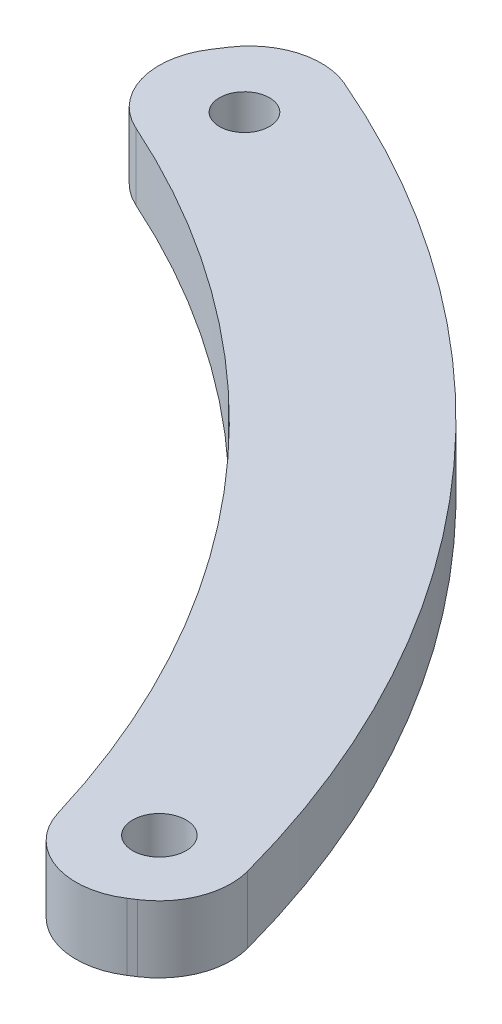
SolidWorks part; units mm, degrees
material "ABS generico"
ref_plane "Piano frontale" through (0, 0, 0) normal (0, 0, 1) x (1, 0, 0)
ref_plane "Piano superiore" through (0, 0, 0) normal (0, 1, 0) x (1, 0, 0)
ref_plane "Piano destro" through (0, 0, 0) normal (1, 0, 0) x (0, 0, -1)
sketch "Schizzo1" plane through (0, 0, 0) normal (0, 1, 0) x (1, 0, 0)
  line L0 (0, 0) -> (5.0353, 3.2628)
  line L2 (-21.2856, 33.3827) -> (-24.5921, 28.3761)
  line L6 (-8.5231, 17.4578) -> (-4.2709, 21.6909) construction
  circle A2 centre (-20.0992, 29.7354) radius 0.9362
  arc A4 (0, 0) -> (-24.5921, 28.3761) centre (-37.0866, -7.2967) ccw
  arc A5 (5.0353, 3.2628) -> (-21.2856, 33.3827) centre (-35.6206, -5.7047) ccw
  circle A6 centre (1.7458, 4.706) radius 1
  arc A7 (2.5176, 1.6314) -> (-22.9388, 30.8794) centre (-36.3444, -6.4906) ccw construction
  point P15 (-6.397, 19.5743)
  dimension "D3" = 2
  dimension "D4" = 3
  dimension "D1" = 6
  dimension "D2" = 40
  dimension "D5" = 3
  dimension "D6" = 6
  dimension "D7" = 6
extrude "Estrusione-Estrusione1" add sketch "Schizzo1" along normal blind 2.5
fillet "Raccordo1" radius 2.7 4 edges at (0, 1.25, 0) (5.0353, 1.25, -3.2628) (-24.5921, 1.25, -28.3761) (-21.2856, 1.25, -33.3827)
